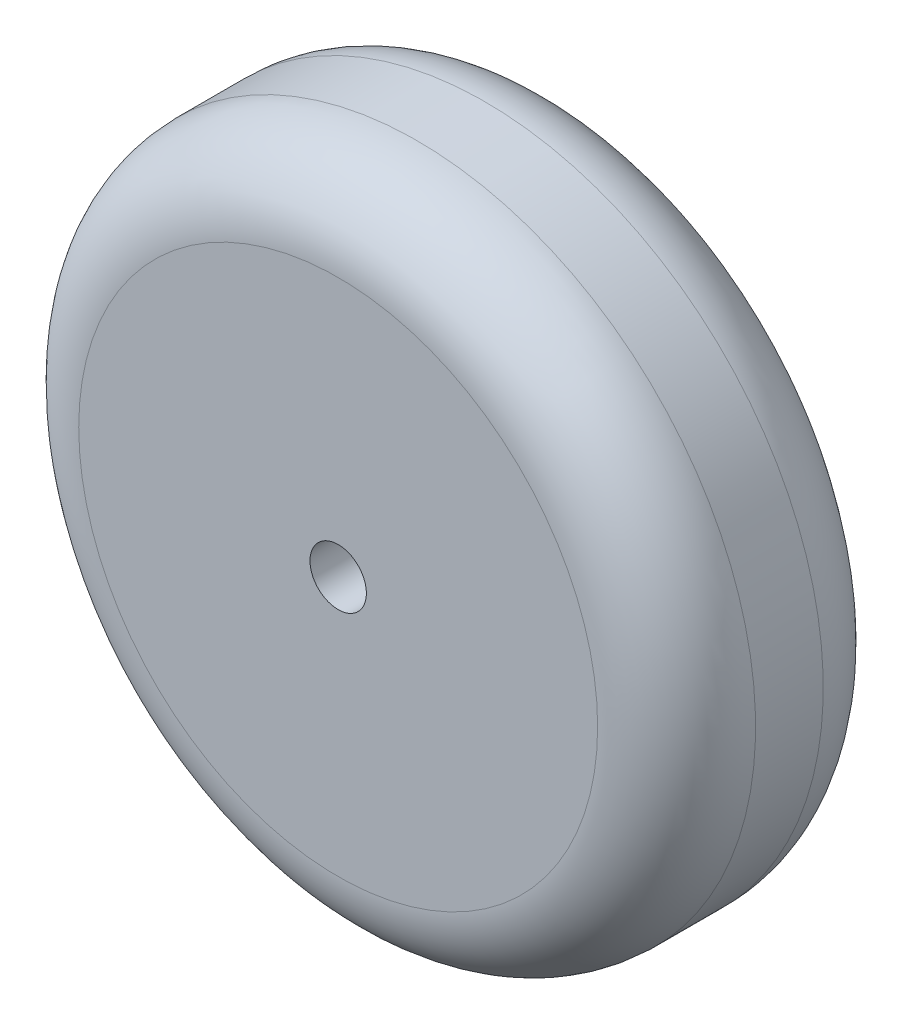
SolidWorks part; units mm, degrees
ref_plane "Front Plane" through (0, 0, 0) normal (0, 0, 1) x (1, 0, 0)
ref_plane "Top Plane" through (0, 0, 0) normal (0, 1, 0) x (1, 0, 0)
ref_plane "Right Plane" through (0, 0, 0) normal (1, 0, 0) x (0, 0, -1)
sketch "Sketch1" plane through (0, 0, 0) normal (1, 0, 0) x (0, 0, -1)
  line L0 (0, 0) -> (0, 73.349) construction
  line L1 (-25.4, 0) -> (-25.4, 58.42)
  line L2 (25.4, 0) -> (25.4, 58.42)
  line L3 (-25.4, 0) -> (25.4, 0)
  line L4 (-7.62, 76.2) -> (7.62, 76.2)
  line L5 (37.2201, 0) -> (-48.2, 0) construction
  arc A0 (25.4, 58.42) -> (7.62, 76.2) centre (7.62, 58.42) ccw
  arc A1 (-25.4, 58.42) -> (-7.62, 76.2) centre (-7.62, 58.42) cw
  point P2 (0, 0)
  point P12 (25.4, 76.2)
  point P15 (-25.4, 76.2)
  dimension "D3" = 76.2
  dimension "D4" = 17.78
  dimension "D1" = 50.8
  dimension "D2" = 50.8
revolve "Revolve2" add sketch "Sketch1" angle 360 about L5
sketch "Sketch2" plane through (0, 0, 0) normal (0, 0, 1) x (1, 0, 0)
  circle A0 centre (0, 0) radius 6.35
  dimension "D1" = 12.7
extrude "Cut-Extrude1" cut sketch "Sketch2" against normal blind 134.62 and the other way blind 108.458
